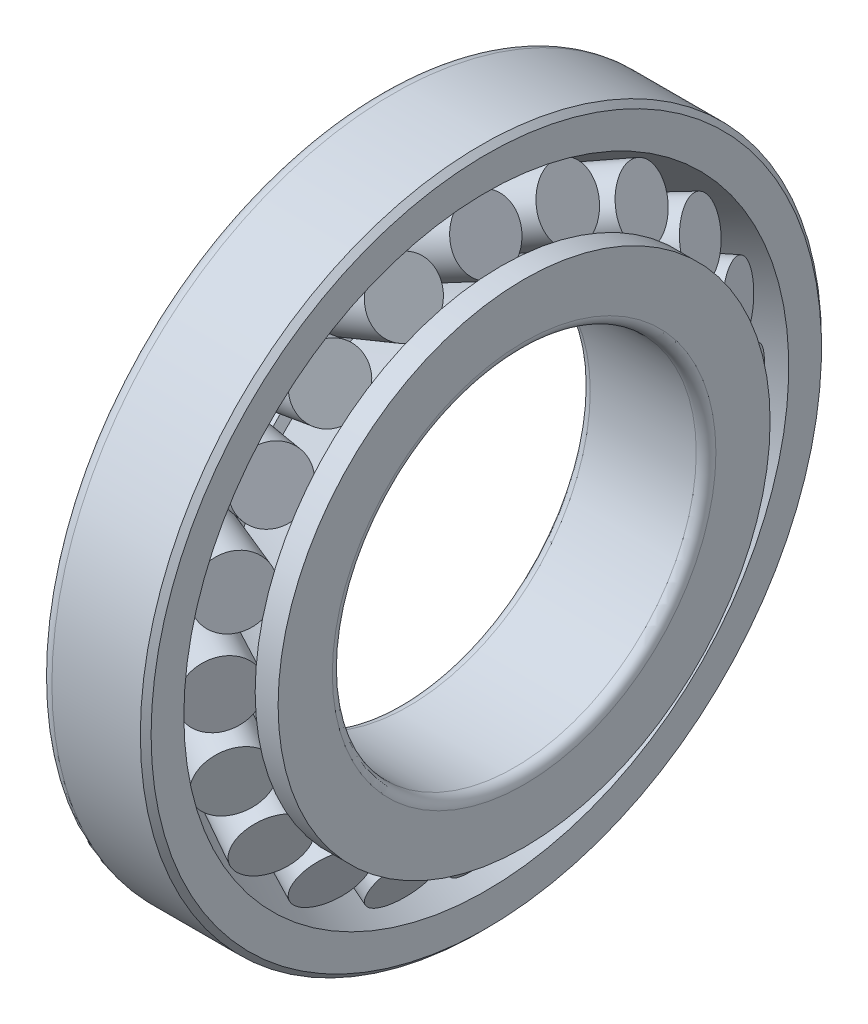
SolidWorks part; units mm, degrees
ref_plane "Front Plane" through (0, 0, 0) normal (0, 0, 1) x (1, 0, 0)
ref_plane "Top Plane" through (0, 0, 0) normal (0, 1, 0) x (1, 0, 0)
ref_plane "Right Plane" through (0, 0, 0) normal (1, 0, 0) x (0, 0, -1)
sketch "Sketch1" plane through (0, 0, 0) normal (0, 0, 1) x (1, 0, 0)
  line L0 (0, 0) -> (50000, 0) construction
  line L1 (-56.3715, 75) -> (-23.7283, 92.3567)
  line L2 (-23.7283, 92.3567) -> (-23.7283, 102.3567)
  line L3 (-23.7283, 102.3567) -> (-25.3715, 104)
  line L4 (-25.3715, 104) -> (-52.3715, 104)
  line L5 (-56.3715, 100) -> (-56.3715, 75)
  arc A0 (-52.3715, 104) -> (-56.3715, 100) centre (-52.3715, 100) ccw
  dimension "D3" = 4
  dimension "D1" = 28
  dimension "D2" = 45
  dimension "D4" = 27
  dimension "D5" = 75
  dimension "D6" = 25
  dimension "D7" = 10
revolve "Revolve1" add sketch "Sketch1" angle 360 about L0
sketch "Sketch2" plane through (0, 0, 0) normal (0, 0, 1) x (1, 0, 0)
  line L2 (-51.5282, 77.5752) -> (-46.8335, 68.7458)
  line L3 (-46.8335, 68.7458) -> (-23.8769, 80.952)
  line L4 (-51.5282, 77.5752) -> (-28.5716, 89.7815)
  line L5 (-28.5716, 89.7815) -> (-23.8769, 80.952)
  line L6 (-71.9411, 40.9728) -> (-72.1675, 40.7464) construction
  point P7 (-40.0499, 83.6784)
  dimension "D1" = 40.0499
  dimension "D2" = 26
  dimension "D3" = 10
revolve "Revolve2" add sketch "Sketch2" angle 360 about L3
sketch "Sketch4" plane through (0, 0, 0) normal (0, 0, 1) x (1, 0, 0)
  line L2 (-42.1388, 59.9163) -> (-19.1821, 72.1225) construction
  line L3 (-43.5472, 62.5651) -> (-42.1388, 59.9163)
  line L5 (-42.1388, 59.9163) -> (-19.1821, 72.1225)
  line L6 (0, 0) -> (50000, 0) construction
  line L7 (-43.5472, 62.5651) -> (-50.5472, 62.5651)
  line L8 (-50.5472, 62.5651) -> (-50.5472, 58.5651)
  line L9 (-19.1821, 75.1225) -> (-12.1821, 75.1225)
  line L10 (-12.1821, 75.1225) -> (-12.1821, 58.5651)
  line L11 (-15.1821, 55.5651) -> (-47.5472, 55.5651)
  line L12 (-19.1821, 72.1225) -> (-19.1821, 75.1225)
  arc A0 (-12.1821, 58.5651) -> (-15.1821, 55.5651) centre (-15.1821, 58.5651) cw
  arc A1 (-50.5472, 58.5651) -> (-47.5472, 55.5651) centre (-47.5472, 58.5651) ccw
  dimension "D3" = 3
  dimension "D1" = 3
  dimension "D2" = 3
  dimension "D4" = 38.3651
  dimension "D5" = 7
  dimension "D6" = 7
  dimension "D7" = 7
revolve "Revolve6" add sketch "Sketch4" angle 360 about L6
pattern_circular "CirPattern3" count 20 over 360 about axis through (0, 0, 0) along (1, 0, 0) of bodies 102
scale "Scale1" bodies to scale 106 104 102 122 121 120 119 118 117 116 115 114 113 112 111 110 109 108 107 101 105 103 scale about origin uniform scaling yes scale factor 0.316667
scale "Scale3" bodies to scale 142 144 136 135 134 133 137 138 139 140 141 123 143 124 125 126 127 128 129 130 131 132 scale about origin uniform scaling yes scale factor 1.1
